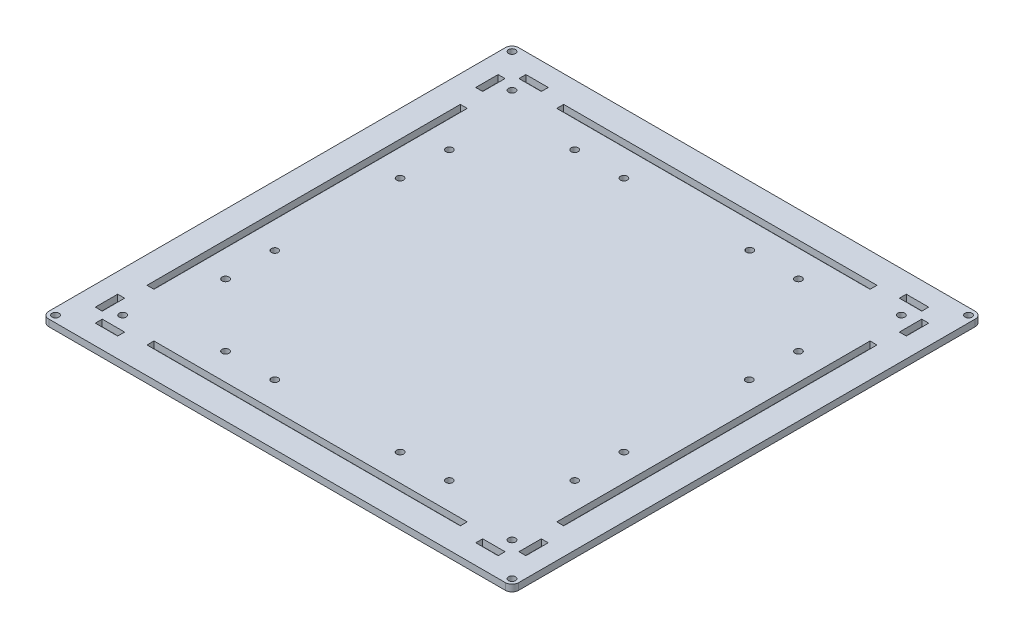
SolidWorks part; units mm, degrees
ref_plane "前视基准面" through (0, 0, 0) normal (0, 0, 1) x (1, 0, 0)
ref_plane "上视基准面" through (0, 0, 0) normal (0, 1, 0) x (1, 0, 0)
ref_plane "右视基准面" through (0, 0, 0) normal (1, 0, 0) x (0, 0, -1)
sketch "草图3" plane through (0, 0, 0) normal (0, 1, 0) x (1, 0, 0)
  line L0 (0, 3) -> (0, 15)
  line L1 (3, 0) -> (207, 0)
  line L2 (0, 3) -> (0, 207)
  line L3 (3, 210) -> (207, 210)
  line L4 (210, 3) -> (210, 207)
  line L5 (0, 15) -> (15, 15) construction
  line L6 (15, 15) -> (15, 0) construction
  line L7 (207, 210) -> (195, 210)
  line L8 (195, 210) -> (195, 195) construction
  line L9 (195, 195) -> (210, 195) construction
  line L11 (195, 195) -> (15, 195)
  line L12 (195, 195) -> (195, 15)
  line L13 (195, 15) -> (15, 15)
  line L14 (15, 195) -> (15, 15)
  line L15 (0, 195) -> (15, 195) construction
  line L16 (0, 195) -> (0, 207)
  line L17 (3, 210) -> (15, 210)
  line L18 (15, 195) -> (15, 210) construction
  line L19 (195, 15) -> (198.1, 15) construction
  line L20 (195, 15) -> (195, 0) construction
  line L21 (195, 0) -> (207, 0)
  line L22 (210, 15) -> (210, 3)
  line L23 (11.9, 175) -> (11.9, 35)
  line L24 (25, 8.8) -> (15, 8.8)
  line L25 (15, 8.8) -> (15, 11.9)
  line L26 (35, 11.9) -> (175, 11.9)
  line L27 (175, 11.9) -> (185, 11.9) construction
  line L28 (15, 11.9) -> (25, 11.9)
  line L29 (198.1, 35) -> (198.1, 175)
  line L30 (35, 11.9) -> (35, 15)
  line L31 (15, 195) -> (35, 195)
  line L32 (175, 198.1) -> (35, 198.1)
  line L33 (195, 195) -> (195, 175)
  line L34 (195, 195) -> (195, 165)
  line L35 (3, 0) -> (3, 3) construction
  line L36 (195, 165) -> (178, 165) construction
  line L37 (3, 210) -> (3, 207) construction
  line L38 (178, 165) -> (178, 123) construction
  line L39 (207, 210) -> (207, 207) construction
  line L40 (178, 123) -> (195, 123) construction
  line L41 (207, 0) -> (207, 3) construction
  line L42 (15, 195) -> (18, 195)
  line L43 (18, 195) -> (18, 192) construction
  line L44 (195, 195) -> (192, 195)
  line L45 (192, 195) -> (192, 192) construction
  line L46 (195, 15) -> (192, 15)
  line L47 (192, 15) -> (192, 18) construction
  line L48 (15, 15) -> (18, 15)
  line L49 (18, 15) -> (18, 18) construction
  line L50 (195, 195) -> (175, 195)
  line L51 (175, 195) -> (175, 198.1)
  line L52 (35, 195) -> (35, 198.1)
  line L53 (195, 175) -> (198.1, 175)
  line L54 (195, 15) -> (195, 35)
  line L55 (195, 35) -> (198.1, 35)
  line L56 (195, 15) -> (175, 15)
  line L57 (175, 15) -> (175, 11.9)
  line L58 (15, 15) -> (15, 35)
  line L59 (15, 35) -> (11.9, 35)
  line L60 (15, 195) -> (15, 175)
  line L61 (15, 175) -> (11.9, 175)
  line L62 (11.9, 25) -> (11.9, 15)
  line L63 (11.9, 15) -> (8.8, 15)
  line L64 (8.8, 15) -> (8.8, 25)
  line L66 (8.8, 25) -> (11.9, 25)
  line L67 (25, 8.8) -> (25, 11.9)
  line L68 (195, 11.9) -> (185, 11.9)
  line L69 (25, 11.9) -> (35, 11.9) construction
  line L70 (11.9, 35) -> (11.9, 25) construction
  line L71 (198.1, 35) -> (198.1, 15) construction
  line L72 (195, 11.9) -> (195, 8.8)
  line L73 (195, 8.8) -> (185, 8.8)
  line L74 (185, 8.8) -> (185, 11.9)
  line L75 (201.2, 15) -> (210, 15) construction
  line L76 (198.1, 25) -> (201.2, 25)
  line L77 (201.2, 15) -> (198.1, 15) construction
  line L78 (201.2, 25) -> (201.2, 15)
  line L79 (201.2, 15) -> (198.1, 15)
  line L80 (198.1, 15) -> (198.1, 25)
  line L81 (198.1, 175) -> (198.1, 195) construction
  line L82 (198.1, 195) -> (201.2, 195)
  line L83 (198.1, 195) -> (198.1, 185)
  line L84 (198.1, 185) -> (201.2, 185)
  line L85 (201.2, 185) -> (201.2, 195)
  line L86 (175, 198.1) -> (195, 198.1) construction
  line L87 (195, 198.1) -> (185, 198.1)
  line L88 (185, 198.1) -> (185, 201.2)
  line L89 (185, 201.2) -> (195, 201.2)
  line L90 (195, 201.2) -> (195, 198.1)
  line L91 (35, 198.1) -> (15, 198.1) construction
  line L92 (15, 198.1) -> (15, 201.2)
  line L93 (15, 198.1) -> (25, 198.1)
  line L94 (25, 198.1) -> (25, 201.2)
  line L95 (25, 201.2) -> (15, 201.2)
  line L96 (11.9, 175) -> (11.9, 195) construction
  line L97 (11.9, 195) -> (11.9, 185)
  line L98 (11.9, 185) -> (8.8, 185)
  line L99 (8.8, 185) -> (8.8, 195)
  line L100 (8.8, 195) -> (11.9, 195)
  line L101 (3, 3) -> (0, 3) construction
  line L102 (3, 207) -> (0, 207) construction
  line L103 (207, 207) -> (210, 207) construction
  line L104 (207, 3) -> (210, 3) construction
  line L105 (178, 165) -> (188, 165) construction
  line L106 (188, 165) -> (188, 123) construction
  line L107 (178, 165) -> (183, 165) construction
  line L109 (178, 165) -> (178, 155) construction
  line L110 (178, 155) -> (181.45, 155) construction
  line L111 (178, 123) -> (178, 133) construction
  line L112 (178, 133) -> (181.45, 133) construction
  line L113 (195, 15) -> (195, 45)
  line L114 (195, 45) -> (178, 45) construction
  line L115 (178, 45) -> (178, 87) construction
  line L116 (178, 87) -> (195, 87) construction
  line L117 (178, 87) -> (188, 87) construction
  line L118 (188, 87) -> (188, 45) construction
  line L119 (178, 87) -> (178, 77) construction
  line L120 (178, 77) -> (188, 77) construction
  line L121 (178, 45) -> (178, 55) construction
  line L122 (178, 55) -> (188, 55) construction
  line L123 (195, 15) -> (165, 15)
  line L124 (165, 15) -> (165, 32) construction
  line L125 (165, 32) -> (123, 32) construction
  line L126 (123, 32) -> (123, 15) construction
  line L127 (123, 32) -> (123, 22)
  line L128 (123, 22) -> (165, 22) construction
  line L129 (123, 32) -> (133, 32) construction
  line L130 (133, 32) -> (133, 22) construction
  line L131 (165, 32) -> (155, 32) construction
  line L132 (155, 32) -> (155, 22) construction
  line L133 (178, 133) -> (188, 133) construction
  line L134 (178, 155) -> (188, 155) construction
  line L135 (15, 15) -> (45, 15)
  line L136 (45, 15) -> (45, 32) construction
  line L137 (45, 32) -> (87, 32) construction
  line L138 (87, 32) -> (87, 15) construction
  line L139 (45, 32) -> (45, 22) construction
  line L140 (45, 22) -> (87, 22) construction
  line L141 (45, 32) -> (55, 32) construction
  line L142 (55, 32) -> (55, 22) construction
  line L143 (87, 32) -> (77, 32) construction
  line L144 (77, 32) -> (77, 22) construction
  line L145 (15, 15) -> (15, 45)
  line L146 (15, 45) -> (32, 45) construction
  line L147 (32, 45) -> (32, 87) construction
  line L148 (32, 87) -> (15, 87) construction
  line L149 (15, 87) -> (32, 87)
  line L150 (32, 87) -> (22, 87)
  line L151 (22, 87) -> (22, 45) construction
  line L152 (32, 45) -> (32, 55) construction
  line L153 (32, 55) -> (22, 55) construction
  line L154 (32, 87) -> (32, 77)
  line L155 (32, 77) -> (22, 77) construction
  line L156 (15, 195) -> (15, 165)
  line L157 (15, 165) -> (32, 165) construction
  line L158 (32, 165) -> (32, 123) construction
  line L159 (32, 123) -> (15, 123) construction
  line L160 (32, 165) -> (22, 165) construction
  line L161 (22, 165) -> (22, 123) construction
  line L162 (32, 165) -> (32, 155) construction
  line L163 (32, 155) -> (22, 155) construction
  line L164 (32, 123) -> (32, 133)
  line L165 (32, 133) -> (22, 133) construction
  line L166 (195, 195) -> (165, 195)
  line L167 (165, 195) -> (165, 178) construction
  line L168 (165, 178) -> (123, 178) construction
  line L169 (123, 178) -> (123, 195) construction
  line L170 (123, 178) -> (123, 188) construction
  line L171 (123, 188) -> (165, 188) construction
  line L172 (165, 178) -> (155, 178) construction
  line L173 (155, 178) -> (155, 188) construction
  line L174 (123, 178) -> (133, 178)
  line L175 (133, 178) -> (133, 188)
  line L176 (15, 195) -> (45, 195)
  line L177 (45, 195) -> (45, 178) construction
  line L178 (45, 178) -> (87, 178) construction
  line L179 (87, 178) -> (87, 195) construction
  line L180 (45, 178) -> (45, 188) construction
  line L181 (45, 188) -> (87, 188) construction
  line L182 (87, 178) -> (77, 178) construction
  line L183 (77, 178) -> (77, 188) construction
  line L184 (45, 178) -> (55, 178) construction
  line L185 (55, 178) -> (55, 188) construction
  circle A0 centre (3, 3) radius 1.55
  circle A1 centre (3, 207) radius 1.55
  circle A2 centre (207, 207) radius 1.55
  circle A3 centre (207, 3) radius 1.55
  circle A4 centre (18, 192) radius 1.55
  circle A5 centre (192, 192) radius 1.55
  circle A6 centre (192, 18) radius 1.55
  circle A7 centre (18, 18) radius 1.55
  arc A8 (207, 0) -> (210, 3) centre (207, 3) ccw
  arc A9 (210, 207) -> (207, 210) centre (207, 207) ccw
  arc A10 (0, 207) -> (3, 210) centre (3, 207) cw
  arc A11 (0, 3) -> (3, 0) centre (3, 3) ccw
  circle A12 centre (183, 133) radius 1.55
  circle A13 centre (183, 155) radius 1.55
  circle A14 centre (183, 55) radius 1.55
  circle A15 centre (183, 77) radius 1.55
  circle A16 centre (133, 27) radius 1.55
  circle A17 centre (155, 27) radius 1.55
  circle A18 centre (55, 27) radius 1.55
  circle A19 centre (77, 27) radius 1.55
  circle A20 centre (27, 77) radius 1.55
  circle A21 centre (27, 55) radius 1.55
  circle A22 centre (27, 155) radius 1.55
  circle A23 centre (27, 133) radius 1.55
  circle A24 centre (133, 183.2525) radius 1.55
  circle A25 centre (155, 183) radius 1.55
  circle A26 centre (55, 183) radius 1.55
  circle A27 centre (77, 183) radius 1.55
extrude "凸台-拉伸1" add sketch "草图3" along normal blind 3
